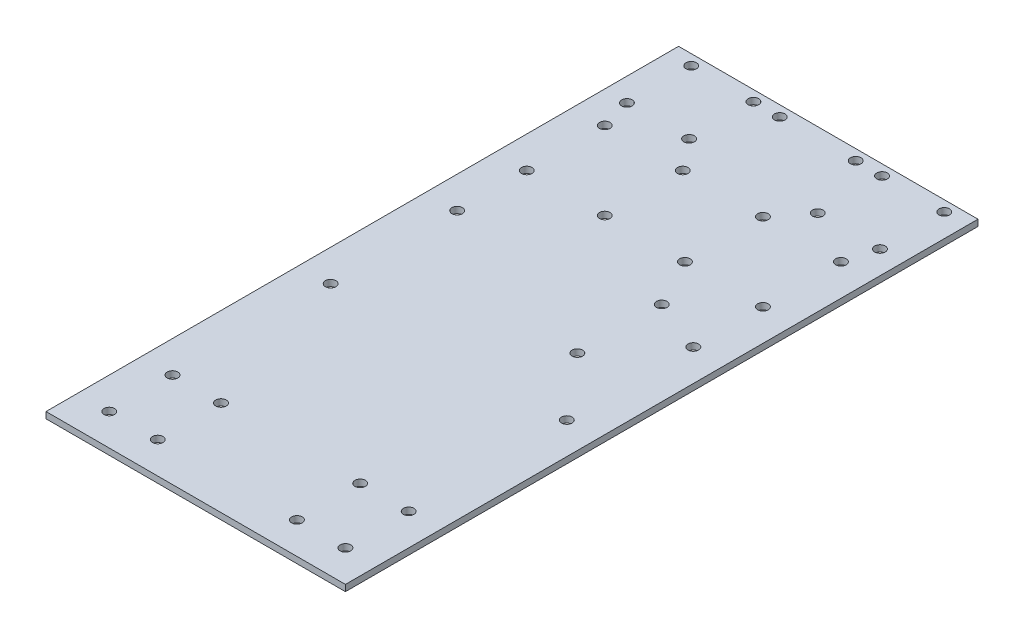
SolidWorks part; units mm, degrees
ref_plane "前视基准面" through (0, 0, 0) normal (0, 0, 1) x (1, 0, 0)
ref_plane "上视基准面" through (0, 0, 0) normal (0, 1, 0) x (1, 0, 0)
ref_plane "右视基准面" through (0, 0, 0) normal (1, 0, 0) x (0, 0, -1)
sketch "草图1" plane through (0, 0, 0) normal (0, 1, 0) x (1, 0, 0)
  line L1 (-71, 150) -> (71, 150)
  line L2 (-71, 150) -> (-71, -150)
  line L3 (-71, -150) -> (71, -150)
  line L4 (71, 150) -> (71, -150)
  point P7 (-792.2601, 315.3251)
  dimension "D1" = 150
  dimension "D2" = 150
  dimension "D3" = 142
  dimension "D4" = 71
extrude "凸台-拉伸1" add sketch "草图1" along normal blind 3
sketch "草图2" plane through (0, 3, 0) normal (0, 1, 0) x (1, 0, 0)
  line L0 (-71, 150) -> (-71, -150) construction
  line L2 (71, 150) -> (-71, 150) construction
  circle A0 centre (-60, 114.5) radius 2.5
  circle A1 centre (-60, 145) radius 2.5
  circle A2 centre (-30.5, 145) radius 2.5
  circle A3 centre (-30.5, 114.5) radius 2.5
  circle A4 centre (-18, 145) radius 2.5
  dimension "D1" = 11
  dimension "D3" = 5
  dimension "D4" = 5
  dimension "D7" = 5
  dimension "D8" = 5
  dimension "D10" = 5
  dimension "D2" = 35.5
  dimension "D5" = 5
  dimension "D6" = 40.5
  dimension "D9" = 53
extrude "切除-拉伸1" cut sketch "草图2" against normal blind 3
mirror "镜向1" about plane through (0, 0, 0) normal (1, 0, 0) of "切除-拉伸1"
sketch "草图3" plane through (0, 3, 0) normal (0, 1, 0) x (1, 0, 0)
  line L0 (-71, 150) -> (-71, -150) construction
  line L1 (71, 150) -> (-71, 150) construction
  circle A0 centre (-56, 100) radius 2.5
  circle A1 centre (-19, 100) radius 2.5
  circle A2 centre (-56, 63) radius 2.5
  circle A3 centre (-19, 63) radius 2.5
  dimension "D1" = 5
  dimension "D2" = 5
  dimension "D3" = 5
  dimension "D4" = 5
  dimension "D5" = 15
  dimension "D6" = 15
  dimension "D7" = 52
  dimension "D8" = 52
  dimension "D9" = 50
  dimension "D10" = 37
extrude "切除-拉伸2" cut sketch "草图3" against normal blind 3
mirror "镜向2" about plane through (0, 0, 0) normal (1, 0, 0) of "切除-拉伸2"
sketch "草图4" plane through (0, 3, 0) normal (0, 1, 0) x (1, 0, 0)
  line L0 (71, -150) -> (71, 150) construction
  line L1 (71, 150) -> (-71, 150) construction
  circle A0 centre (31, 40) radius 2.5
  circle A1 centre (31, 0) radius 2.5
  dimension "D1" = 5
  dimension "D2" = 5
  dimension "D3" = 40
  dimension "D4" = 110
  dimension "D5" = 40
extrude "切除-拉伸3" cut sketch "草图4" against normal blind 3
sketch "草图5" plane through (0, 3, 0) normal (0, 1, 0) x (1, 0, 0)
  line L0 (-71, 150) -> (-71, -150) construction
  line L1 (71, 150) -> (-71, 150) construction
  circle A0 centre (-56, -30) radius 2.5
  circle A1 centre (-56, 30) radius 2.5
  point P4 (0, 0)
  dimension "D2" = 5
  dimension "D1" = 15
  dimension "D3" = 120
  dimension "D4" = 60
extrude "切除-拉伸4" cut sketch "草图5" against normal blind 3
mirror "镜向3" about plane through (0, 0, 0) normal (1, 0, 0) of "切除-拉伸4"
sketch "草图6" plane through (0, 3, 0) normal (0, 1, 0) x (1, 0, 0)
  line L0 (-71, -150) -> (71, -150) construction
  line L1 (-71, 150) -> (-71, -150) construction
  circle A0 centre (-33, -105) radius 2.5
  circle A1 centre (-33, -135) radius 2.5
  circle A2 centre (-56, -135) radius 2.5
  circle A3 centre (-56, -105) radius 2.5
  point P10 (0, 0)
  point P11 (0, 0)
  point P12 (-71, -129.5017)
  point P15 (0, 0)
  point P16 (0, 0)
  point P17 (0, 0)
  point P18 (0, 0)
  dimension "D3" = 5
  dimension "D1" = 15
  dimension "D2" = 15
  dimension "D4" = 38
  dimension "D5" = 30
extrude "切除-拉伸5" cut sketch "草图6" against normal blind 3
mirror "镜向4" about plane through (0, 0, 0) normal (1, 0, 0) of "切除-拉伸5"
